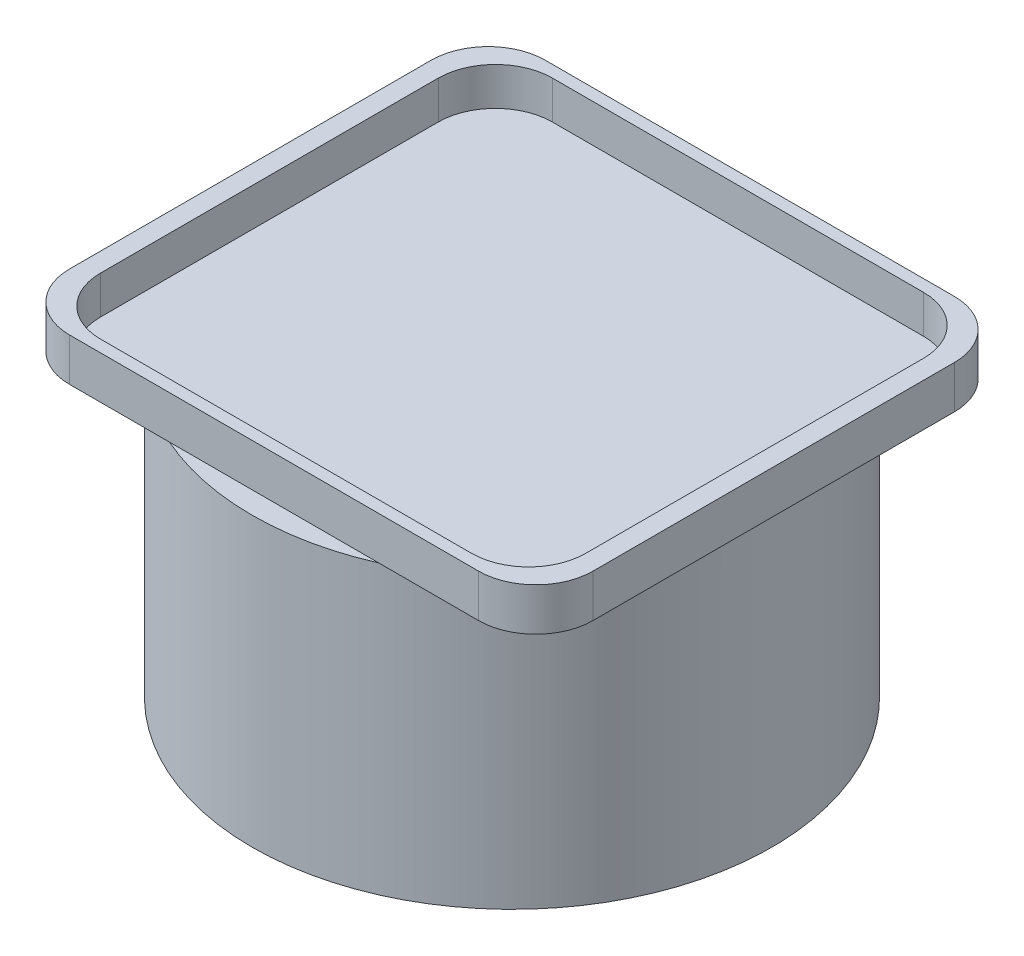
SolidWorks part; units mm, degrees
material "Thornel Mat VMA"
ref_plane "Front" through (0, 0, 0) normal (0, 0, 1) x (1, 0, 0)
ref_plane "Top" through (0, 0, 0) normal (0, 1, 0) x (1, 0, 0)
ref_plane "Right" through (0, 0, 0) normal (1, 0, 0) x (0, 0, -1)
sketch "Sketch1" plane through (0, 0, 0) normal (0, 1, 0) x (1, 0, 0)
  line L1 (-10.922, -12.7) -> (10.922, -12.7)
  line L2 (-13.97, -9.652) -> (-13.97, 9.652)
  line L3 (-10.922, 12.7) -> (10.922, 12.7)
  line L4 (13.97, -9.652) -> (13.97, 9.652)
  line L5 (-13.97, -12.7) -> (13.97, 12.7) construction
  line L6 (-13.97, 12.7) -> (13.97, -12.7) construction
  line L7 (-9.906, -12.065) -> (9.906, -12.065)
  line L8 (-12.954, -9.017) -> (-12.954, 9.017)
  line L9 (-9.906, 12.065) -> (9.906, 12.065)
  line L10 (12.954, -9.017) -> (12.954, 9.017)
  line L11 (-12.954, -12.065) -> (12.954, 12.065) construction
  line L12 (-12.954, 12.065) -> (12.954, -12.065) construction
  arc A0 (-12.954, -9.017) -> (-9.906, -12.065) centre (-9.906, -9.017) ccw
  arc A1 (9.906, -12.065) -> (12.954, -9.017) centre (9.906, -9.017) ccw
  arc A2 (12.954, 9.017) -> (9.906, 12.065) centre (9.906, 9.017) ccw
  arc A3 (-9.906, 12.065) -> (-12.954, 9.017) centre (-9.906, 9.017) ccw
  arc A4 (-13.97, 9.652) -> (-10.922, 12.7) centre (-10.922, 9.652) cw
  arc A5 (10.922, 12.7) -> (13.97, 9.652) centre (10.922, 9.652) cw
  arc A6 (13.97, -9.652) -> (10.922, -12.7) centre (10.922, -9.652) cw
  arc A7 (-10.922, -12.7) -> (-13.97, -9.652) centre (-10.922, -9.652) cw
  point P0 (0, 0)
  point P6 (0, 0)
  dimension "D5" = 3.048
  dimension "D6" = 3.048
  dimension "D1" = 25.4
  dimension "D2" = 27.94
  dimension "D3" = 25.908
  dimension "D4" = 24.13
extrude "Boss-Extrude1" add sketch "Sketch1" along normal blind 2.032
sketch "Sketch2" plane through (0, 0, 0) normal (0, -1, 0) x (1, 0, 0)
  line L4 (-10.922, -12.7) -> (10.922, -12.7)
  line L5 (13.97, -9.652) -> (13.97, 9.652)
  line L6 (10.922, 12.7) -> (-10.922, 12.7)
  line L7 (-13.97, 9.652) -> (-13.97, -9.652)
  line L8 (-10.922, -12.7) -> (10.922, -12.7)
  line L9 (13.97, -9.652) -> (13.97, 9.652)
  line L10 (10.922, 12.7) -> (-10.922, 12.7)
  line L11 (-13.97, 9.652) -> (-13.97, -9.652)
  arc A4 (-13.97, -9.652) -> (-10.922, -12.7) centre (-10.922, -9.652) ccw
  arc A5 (10.922, -12.7) -> (13.97, -9.652) centre (10.922, -9.652) ccw
  arc A6 (13.97, 9.652) -> (10.922, 12.7) centre (10.922, 9.652) ccw
  arc A7 (-10.922, 12.7) -> (-13.97, 9.652) centre (-10.922, 9.652) ccw
  arc A8 (-13.97, -9.652) -> (-10.922, -12.7) centre (-10.922, -9.652) ccw
  arc A9 (10.922, -12.7) -> (13.97, -9.652) centre (10.922, -9.652) ccw
  arc A10 (13.97, 9.652) -> (10.922, 12.7) centre (10.922, 9.652) ccw
  arc A11 (-10.922, 12.7) -> (-13.97, 9.652) centre (-10.922, 9.652) ccw
  dimension "D1" = 0
extrude "Boss-Extrude2" add sketch "Sketch2" along normal blind 0.254
sketch "Sketch3" plane through (0, -0.254, 0) normal (0, -1, 0) x (1, 0, 0)
  circle A0 centre (0, 0) radius 13.8748
  dimension "D1" = 27.7495
extrude "Boss-Extrude3" add sketch "Sketch3" along normal blind 15.35
